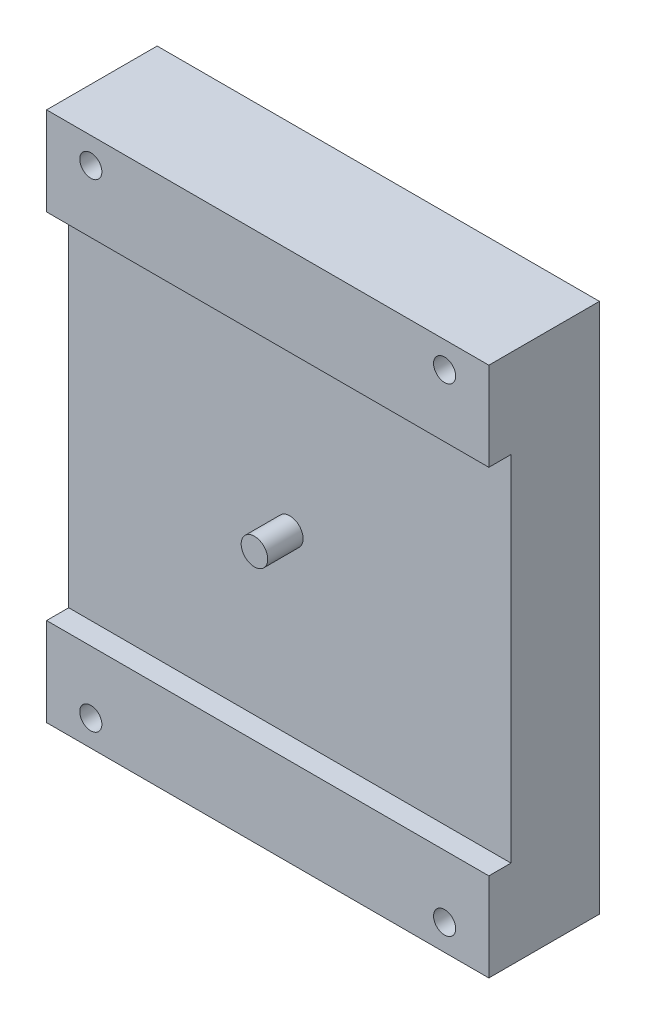
SolidWorks part; units mm, degrees
ref_plane "Ebene vorne" through (0, 0, 0) normal (0, 0, 1) x (1, 0, 0)
ref_plane "Ebene oben" through (0, 0, 0) normal (0, 1, 0) x (1, 0, 0)
ref_plane "Ebene rechts" through (0, 0, 0) normal (1, 0, 0) x (0, 0, -1)
sketch "Skizze1" plane through (0, 0, 0) normal (0, 0, 1) x (1, 0, 0)
  line L1 (0, 0) -> (-50, 0)
  line L2 (0, 0) -> (0, 60)
  line L3 (0, 60) -> (-50, 60)
  line L4 (-50, 0) -> (-50, 60)
  circle A0 centre (-45, 57.05) radius 1.25
  circle A1 centre (-5, 57.05) radius 1.25
  circle A2 centre (-45, 2.95) radius 1.25
  circle A3 centre (-5, 2.95) radius 1.25
  dimension "D4" = 2.5
  dimension "D1" = 60
  dimension "D2" = 50
  dimension "D3" = 2.95
  dimension "D5" = 5
  dimension "D7" = 5
  dimension "D9" = 2.95
  dimension "D11" = 5
  dimension "D6" = 2
  dimension "D8" = 2
  dimension "D10" = 2
extrude "Aufsatz-Linear austragen1" add sketch "Skizze1" along normal blind 10
sketch "Skizze2" plane through (0, 0, 10) normal (0, 0, 1) x (1, 0, 0)
  line L0 (0, 60) -> (-50, 60) construction
  line L1 (-50, 60) -> (-50, 0) construction
  circle A0 centre (-25, 30) radius 1.5
  dimension "D3" = 3
  dimension "D1" = 30
  dimension "D2" = 25
extrude "Aufsatz-Linear austragen2" add sketch "Skizze2" along normal blind 4
sketch "Skizze3" plane through (0, 0, 10) normal (0, 0, 1) x (1, 0, 0)
  line L0 (0, 0) -> (0, 60) construction
  line L1 (-50, 60) -> (0, 60)
  line L2 (-50, 60) -> (-50, 50)
  line L3 (-50, 50) -> (0, 50)
  line L4 (0, 60) -> (0, 50)
  line L5 (-50, 60) -> (-50, 0) construction
  line L6 (0, 0) -> (-50, 0)
  line L7 (0, 0) -> (0, 10)
  line L8 (0, 10) -> (-50, 10)
  line L9 (-50, 0) -> (-50, 10)
  circle A2 centre (-45, 57.05) radius 1.25
  circle A3 centre (-5, 57.05) radius 1.25
  circle A4 centre (-45, 2.95) radius 1.25
  circle A5 centre (-5, 2.95) radius 1.25
  circle A6 centre (-45, 57.05) radius 1.25 construction
  circle A7 centre (-5, 57.05) radius 1.25 construction
  circle A8 centre (-45, 2.95) radius 1.25 construction
  circle A9 centre (-5, 2.95) radius 1.25 construction
  dimension "D1" = 10
  dimension "D2" = 10
extrude "Aufsatz-Linear austragen3" add sketch "Skizze3" along normal blind 2.5
